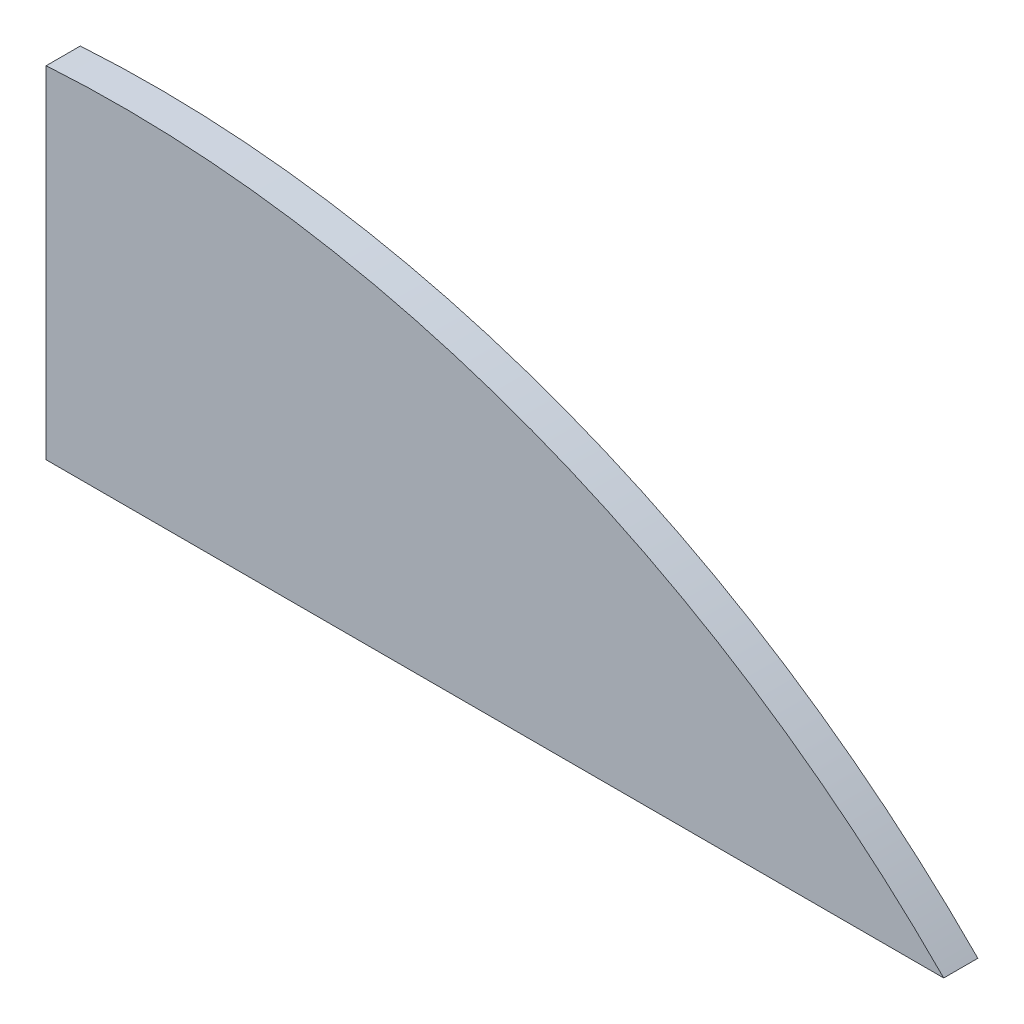
SolidWorks part; units mm, degrees
ref_plane "Front Plane" through (0, 0, 0) normal (0, 0, 1) x (1, 0, 0)
ref_plane "Top Plane" through (0, 0, 0) normal (0, 1, 0) x (1, 0, 0)
ref_plane "Right Plane" through (0, 0, 0) normal (1, 0, 0) x (0, 0, -1)
sketch "Sketch1" plane through (0, 0, 0) normal (0, 0, 1) x (1, 0, 0)
  line L0 (0, 0) -> (0, 10)
  line L1 (0, 0) -> (26.3, 0)
  arc A0 (0, 10) -> (26.3, 0) centre (2.2027, -23.7915) cw
  point P0 (0, 0)
  dimension "D3" = 33.8632
  dimension "D1" = 10
  dimension "D2" = 26.3
extrude "Boss-Extrude1" add sketch "Sketch1" along normal blind 1
